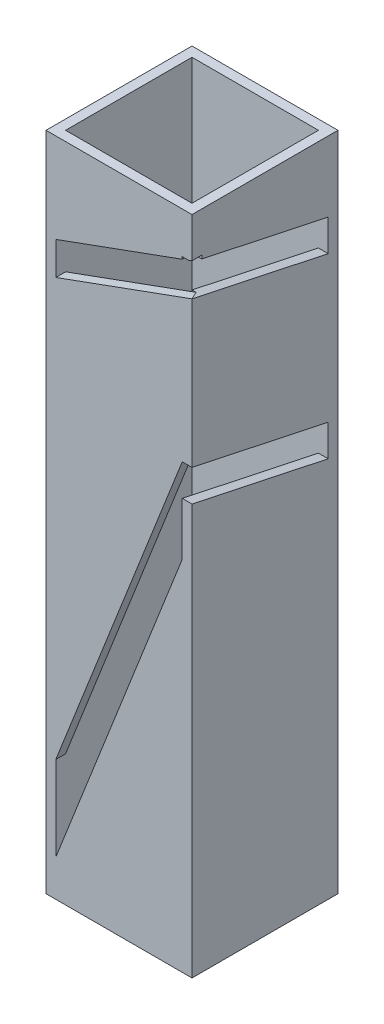
SolidWorks part; units mm, degrees
ref_plane "Front Plane" through (0, 0, 0) normal (0, 0, 1) x (1, 0, 0)
ref_plane "Top Plane" through (0, 0, 0) normal (0, 1, 0) x (1, 0, 0)
ref_plane "Right Plane" through (0, 0, 0) normal (1, 0, 0) x (0, 0, -1)
sketch "Sketch1" plane through (0, 0, 0) normal (0, 1, 0) x (1, 0, 0)
  line L1 (19.431, -19.431) -> (-19.431, -19.431)
  line L2 (19.431, -19.431) -> (19.431, 19.431)
  line L3 (19.431, 19.431) -> (-19.431, 19.431)
  line L4 (-19.431, -19.431) -> (-19.431, 19.431)
  line L5 (19.431, -19.431) -> (-19.431, 19.431) construction
  line L6 (19.431, 19.431) -> (-19.431, -19.431) construction
  line L7 (22.431, 22.431) -> (-22.431, 22.431)
  line L8 (22.431, 22.431) -> (22.431, -22.431)
  line L9 (22.431, -22.431) -> (-22.431, -22.431)
  line L10 (-22.431, 22.431) -> (-22.431, -22.431)
  line L11 (22.431, 22.431) -> (-22.431, -22.431) construction
  line L12 (22.431, -22.431) -> (-22.431, 22.431) construction
  point P0 (0, 0)
  point P5 (0, 0)
  dimension "D1" = 38.862
  dimension "D2" = 3
extrude "Boss-Extrude1" add sketch "Sketch1" along normal blind 203.2
sketch "Sketch3" plane through (22.431, 0, 0) normal (1, 0, 0) x (0, 0, -1)
  line L0 (-22.431, 190.5) -> (19.431, 181.602)
  line L1 (-22.431, 203.2) -> (-22.431, 0) construction
  line L2 (19.431, 181.602) -> (19.431, 171.8642)
  line L3 (19.431, 171.8642) -> (-22.431, 180.7622)
  line L4 (-22.431, 190.5) -> (-22.431, 180.7622)
  line L5 (19.431, 203.2) -> (19.431, 0) construction
  line L6 (22.431, 203.2) -> (22.431, 0) construction
  line L7 (-22.431, 126.1602) -> (19.431, 117.2622)
  line L8 (19.431, 117.2622) -> (19.431, 127)
  line L9 (19.431, 127) -> (-22.431, 135.898)
  line L10 (-22.431, 135.898) -> (-22.431, 126.1602)
  line L11 (-1.5, 186.051) -> (-3.4804, 176.7341) construction
  line L12 (-1.5, 131.449) -> (-3.4804, 122.1322) construction
  line L13 (19.431, 171.8642) -> (19.431, 127) construction
  line L15 (-22.431, 203.2) -> (22.431, 203.2) construction
  dimension "D1" = 9.525
  dimension "D2" = 12.7
  dimension "D3" = 78
  dimension "D4" = 102
  dimension "D5" = 76.2
extrude "X Face Cut" cut sketch "Sketch3" against normal up to surface (3 mm away) up to face at (19.431, 101.6, 0)
sketch "Sketch4" plane through (0, 0, 22.431) normal (0, 0, 1) x (1, 0, 0)
  line L0 (22.431, 180.7622) -> (-19.431, 165.5257)
  line L1 (-19.431, 165.5257) -> (-19.431, 175.662)
  line L2 (-19.431, 175.662) -> (22.431, 190.8985)
  line L3 (22.431, 180.7622) -> (22.431, 135.898) construction
  line L5 (1.5, 183.2802) -> (4.7577, 174.3297) construction
  line L6 (-19.431, 203.2) -> (-19.431, 0) construction
  line L7 (22.431, 203.2) -> (22.431, 190.5) construction
  line L8 (22.431, 190.8985) -> (22.431, 180.7622)
  line L9 (19.431, 109.909) -> (-19.431, 11.2521)
  line L10 (-19.431, 11.2521) -> (-19.431, 37.2411)
  line L11 (-19.431, 37.2411) -> (19.431, 135.898)
  line L13 (19.431, 135.898) -> (19.431, 109.909)
  line L14 (0, 60.5806) -> (-8.8622, 64.0715) construction
  line L17 (19.431, 135.898) -> (19.431, 126.1602) construction
  point P24 (0, 0)
  point P25 (22.431, 126.1602)
  point P26 (22.431, 143.4265)
  point P27 (19.431, 135.898)
  point P30 (0, 0)
  dimension "D1" = 70
  dimension "D2" = 9.525
  dimension "D3" = 9.525
  dimension "D4" = 21.5
extrude "Y Face" cut sketch "Sketch4" against normal up to surface (3 mm away) up to face at (9.7155, 129.6462, 19.431)
